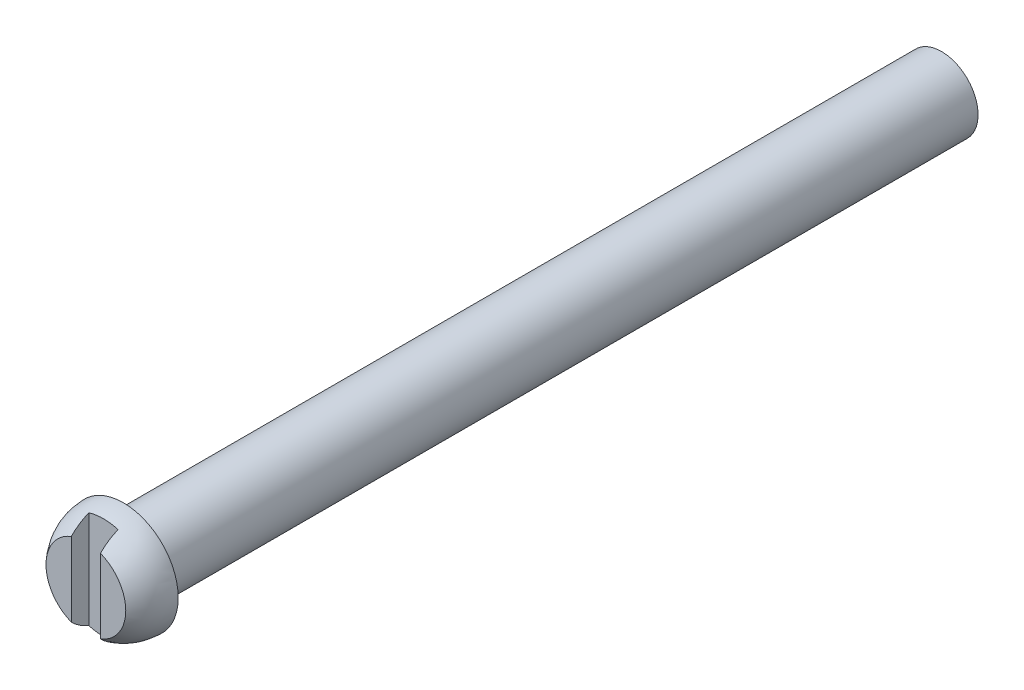
SolidWorks part; units mm, degrees
ref_plane "Front Plane" through (0, 0, 0) normal (0, 0, 1) x (1, 0, 0)
ref_plane "Top Plane" through (0, 0, 0) normal (0, 1, 0) x (1, 0, 0)
ref_plane "Right Plane" through (0, 0, 0) normal (1, 0, 0) x (0, 0, -1)
sketch "Sketch1" plane through (0, 0, 0) normal (0, 0, 1) x (1, 0, 0)
  circle A0 centre (0, 0) radius 3.175
  dimension "D1" = 6.35
extrude "Boss-Extrude1" add sketch "Sketch1" along normal blind 20.32
sketch "Sketch2" plane through (0, 0, 20.32) normal (0, 0, 1) x (1, 0, 0)
  line L0 (0, -4.7625) -> (0, 4.7625)
  line L1 (0, -4.7625) -> (-3.103, -4.7625) construction
  arc A0 (0, -4.7625) -> (0, 4.7625) centre (0, 0) ccw
  dimension "D1" = 9.525
revolve "Revolve1" add sketch "Sketch2" angle 180 about L0
ref_plane "Plane1" through (2.54, 0, 0) normal (1, 0, 0) x (0, 0, -1)
sketch "Sketch3" plane through (2.54, 0, 0) normal (1, 0, 0) x (0, 0, -1)
  line L1 (-25.3415, 4.8464) -> (-23.5855, 4.8464)
  line L2 (-25.3415, 4.8464) -> (-25.3415, -6.8752)
  line L3 (-25.3415, -6.8752) -> (-23.5855, -6.8752)
  line L4 (-23.5855, 4.8464) -> (-23.5855, -6.8752)
extrude "Cut-Extrude1" cut sketch "Sketch3" against normal blind 9.398 and the other way blind 8.382
sketch "Sketch4" plane through (0, 0, 23.5855) normal (0, 0, 1) x (1, 0, 0)
  line L0 (3.4667, 0) -> (1.27, 0) construction
  line L1 (1.27, 5.6131) -> (-1.27, 5.6131)
  line L2 (1.27, 5.6131) -> (1.27, -7.1989)
  line L3 (1.27, -7.1989) -> (-1.27, -7.1989)
  line L4 (-1.27, 5.6131) -> (-1.27, -7.1989)
  line L5 (-1.27, 0) -> (-3.4667, 0) construction
  circle A0 centre (0, 0) radius 3.4667 construction
  dimension "D1" = 2.54
extrude "Cut-Extrude2" cut sketch "Sketch4" against normal blind 1.524
sketch "Sketch5" plane through (0, 0, 0) normal (0, 0, -1) x (-1, 0, 0)
  circle A0 centre (0, 0) radius 3.175
extrude "Boss-Extrude2" add sketch "Sketch5" along normal blind 50.8
